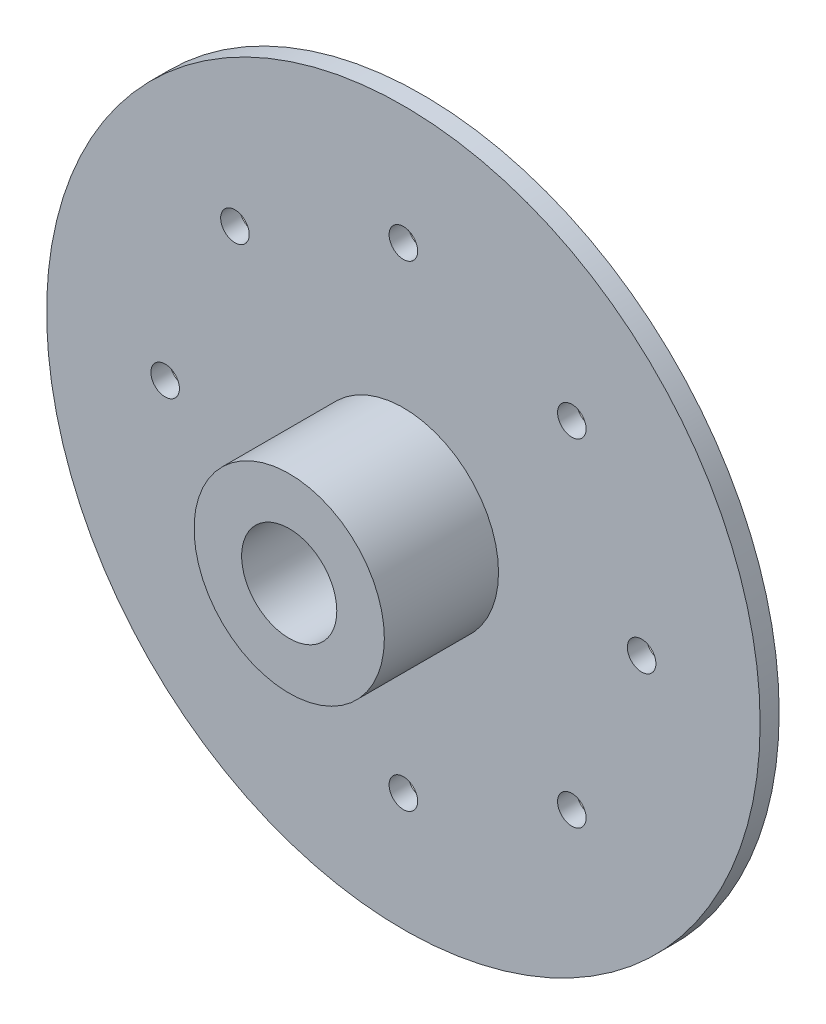
SolidWorks part; units mm, degrees
ref_plane "Front Plane" through (0, 0, 0) normal (0, 0, 1) x (1, 0, 0)
ref_plane "Top Plane" through (0, 0, 0) normal (0, 1, 0) x (1, 0, 0)
ref_plane "Right Plane" through (0, 0, 0) normal (1, 0, 0) x (0, 0, -1)
sketch "Sketch1" plane through (0, 0, 0) normal (0, 0, 1) x (1, 0, 0)
  circle A0 centre (0, 0) radius 37.5
  dimension "D1" = 75
extrude "Boss-Extrude1" add sketch "Sketch1" along normal blind 2
sketch "Sketch2" plane through (0, 0, 2) normal (0, 0, 1) x (1, 0, 0)
  circle A0 centre (0, 25) radius 1.5
  dimension "D1" = 3
  dimension "D2" = 25
extrude "Cut-Extrude1" cut sketch "Sketch2" against normal blind 10
pattern_circular "CirPattern1" count 8 over 360 about axis through (0, -0.0401, 0) along (0, 0, 1) of "Cut-Extrude1"
sketch "Sketch3" plane through (0, 0, 2) normal (0, 0, 1) x (1, 0, 0)
  circle A0 centre (0, 0) radius 10
  circle A1 centre (0, 0) radius 5
  dimension "D1" = 20
  dimension "D2" = 10
extrude "Boss-Extrude2" add sketch "Sketch3" along normal blind 12
